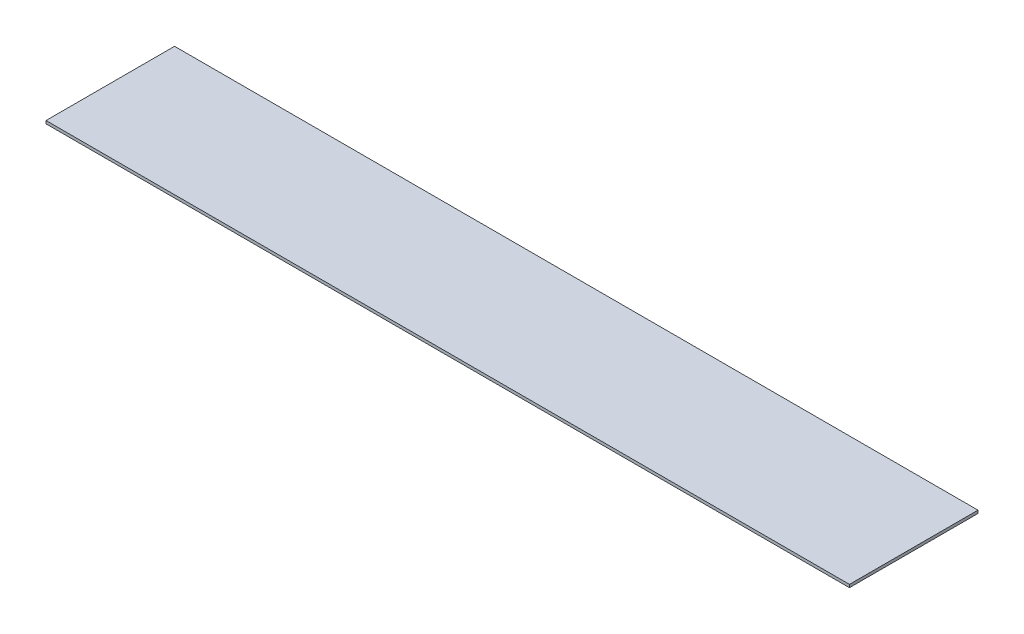
SolidWorks part; units mm, degrees
material "Zirconium"
ref_plane "Front Plane" through (0, 0, 0) normal (0, 0, 1) x (1, 0, 0)
ref_plane "Top Plane" through (0, 0, 0) normal (0, 1, 0) x (1, 0, 0)
ref_plane "Right Plane" through (0, 0, 0) normal (1, 0, 0) x (0, 0, -1)
sketch "Sketch1" plane through (0, 0, 0) normal (0, 1, 0) x (1, 0, 0)
  line L1 (-25, 4) -> (25, 4)
  line L2 (-25, 4) -> (-25, -4)
  line L3 (-25, -4) -> (25, -4)
  line L4 (25, 4) -> (25, -4)
  line L5 (-25, 4) -> (25, -4) construction
  line L6 (-25, -4) -> (25, 4) construction
  point P0 (0, 0)
  dimension "D1" = 8
  dimension "D2" = 50
extrude "Boss-Extrude1" add sketch "Sketch1" along normal blind 0.18
